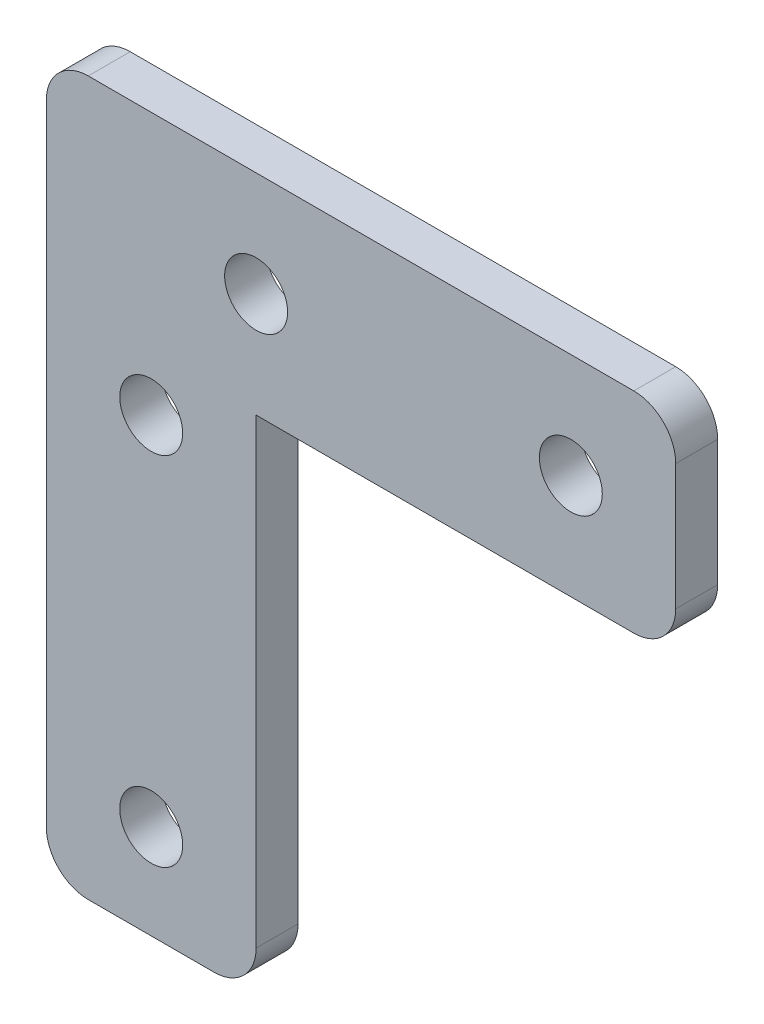
SolidWorks part; units mm, degrees
material "Acrylic (Medium-high impact)"
ref_plane "Front Plane" through (0, 0, 0) normal (0, 0, 1) x (1, 0, 0)
ref_plane "Top Plane" through (0, 0, 0) normal (0, 1, 0) x (1, 0, 0)
ref_plane "Right Plane" through (0, 0, 0) normal (1, 0, 0) x (0, 0, -1)
sketch "Sketch1" plane through (0, 0, 0) normal (0, 0, 1) x (1, 0, 0)
  line L0 (0, -12) -> (0, -7.5) construction
  line L2 (-5, 12) -> (-5, -12)
  line L3 (-5, -12) -> (5, -12)
  line L4 (5, 12) -> (5, -12)
  line L5 (-5, 12) -> (5, -12) construction
  line L6 (-5, -12) -> (5, 12) construction
  line L7 (0, -7.5) -> (0, 9.5) construction
  line L13 (5, 12) -> (25, 12)
  line L14 (25, 12) -> (25, 22)
  line L15 (25, 22) -> (-5, 22)
  line L16 (-5, 22) -> (-5, 12)
  line L17 (25, 17) -> (20, 17) construction
  line L18 (20, 17) -> (5, 17) construction
  circle A0 centre (0, 9.5) radius 1.5
  circle A1 centre (0, -7.5) radius 1.5
  circle A4 centre (5, 17) radius 1.5
  circle A5 centre (20, 17) radius 1.5
  point P0 (0, 0)
  dimension "D5" = 3
  dimension "D6" = 3
  dimension "D11" = 3
  dimension "D12" = 3
  dimension "D1" = 24
  dimension "D2" = 10
  dimension "D3" = 4.5
  dimension "D4" = 17
  dimension "D7" = 20
  dimension "D8" = 10
  dimension "D9" = 5
  dimension "D10" = 15
extrude "Boss-Extrude1" add sketch "Sketch1" along normal blind 2
fillet "Fillet1" radius 2 5 edges at (25, 12, 1) (5, -12, 1) (-5, -12, 1) (-5, 22, 1) (25, 22, 1)
